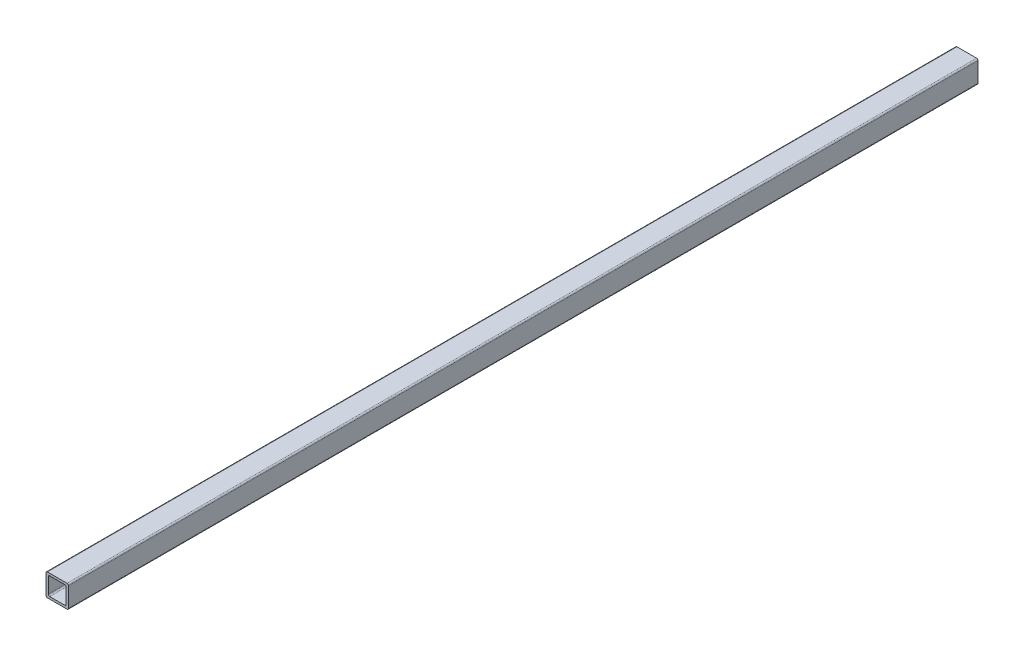
SolidWorks part; units mm, degrees
material "Hexcel AS4C (3000 Filaments)"
ref_plane "Front Plane" through (0, 0, 0) normal (0, 0, 1) x (1, 0, 0)
ref_plane "Top Plane" through (0, 0, 0) normal (0, 1, 0) x (1, 0, 0)
ref_plane "Right Plane" through (0, 0, 0) normal (1, 0, 0) x (0, 0, -1)
sketch "Sketch1" plane through (0, 0, 0) normal (0, 0, 1) x (1, 0, 0)
  line L1 (3.15, -3.15) -> (-3.15, -3.15)
  line L2 (3.15, -3.15) -> (3.15, 3.15)
  line L3 (3.15, 3.15) -> (-3.15, 3.15)
  line L4 (-3.15, -3.15) -> (-3.15, 3.15)
  line L5 (3.15, -3.15) -> (-3.15, 3.15) construction
  line L6 (3.15, 3.15) -> (-3.15, -3.15) construction
  line L7 (3.95, -3.95) -> (-3.95, -3.95)
  line L8 (3.95, -3.95) -> (3.95, 3.95)
  line L9 (3.95, 3.95) -> (-3.95, 3.95)
  line L10 (-3.95, -3.95) -> (-3.95, 3.95)
  line L11 (3.95, -3.95) -> (-3.95, 3.95) construction
  line L12 (3.95, 3.95) -> (-3.95, -3.95) construction
  point P0 (0, 0)
  point P6 (0, 0)
  dimension "D1" = 7.9
  dimension "D2" = 0.8
extrude "Boss-Extrude1" add sketch "Sketch1" along normal blind 320
fillet "Fillet1" radius 0.5 8 edges at (3.95, 3.95, 160) (3.15, 3.15, 160) (3.95, -3.95, 160) (3.15, -3.15, 160) (-3.15, -3.15, 160) (-3.95, -3.95, 160) (-3.95, 3.95, 160) (-3.15, 3.15, 160)
